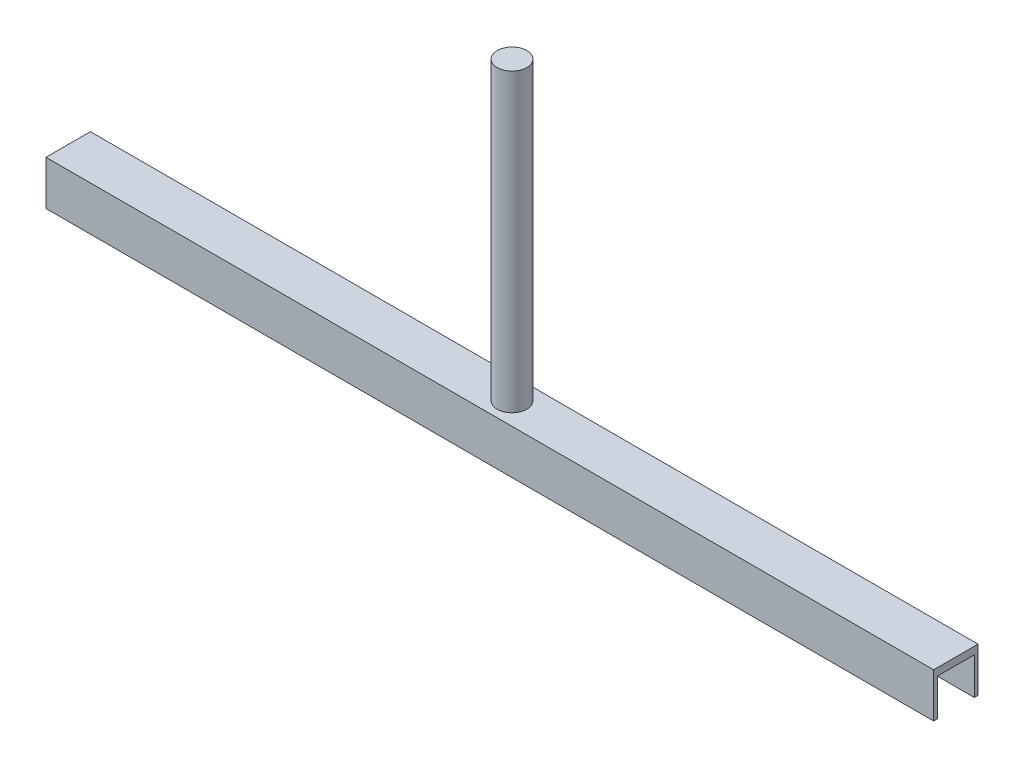
SolidWorks part; units mm, degrees
ref_plane "Front Plane" through (0, 0, 0) normal (0, 0, 1) x (1, 0, 0)
ref_plane "Top Plane" through (0, 0, 0) normal (0, 1, 0) x (1, 0, 0)
ref_plane "Right Plane" through (0, 0, 0) normal (1, 0, 0) x (0, 0, -1)
sketch "Sketch1" plane through (0, 0, 0) normal (0, 1, 0) x (1, 0, 0)
  line L1 (150, -7.5) -> (-150, -7.5)
  line L2 (150, -7.5) -> (150, 7.5)
  line L3 (150, 7.5) -> (-150, 7.5)
  line L4 (-150, -7.5) -> (-150, 7.5)
  line L5 (150, -7.5) -> (-150, 7.5) construction
  line L6 (150, 7.5) -> (-150, -7.5) construction
  point P0 (0, 0)
extrude "Boss-Extrude1" add sketch "Sketch1" along normal blind 15
sketch "Sketch2" plane through (0, 0, 0) normal (0, 1, 0) x (1, 0, 0)
  line L1 (150, -6.25) -> (-150, -6.25)
  line L2 (150, -6.25) -> (150, 6.25)
  line L3 (150, 6.25) -> (-150, 6.25)
  line L4 (-150, -6.25) -> (-150, 6.25)
  line L5 (150, -6.25) -> (-150, 6.25) construction
  line L6 (150, 6.25) -> (-150, -6.25) construction
  point P0 (0, 0)
extrude "Cut-Extrude2" cut sketch "Sketch2" along normal blind 12.5
sketch "Sketch3" plane through (0, 15, 0) normal (0, 1, 0) x (1, 0, 0)
  circle A0 centre (0, 0) radius 5
extrude "Boss-Extrude2" add sketch "Sketch3" along normal blind 100
